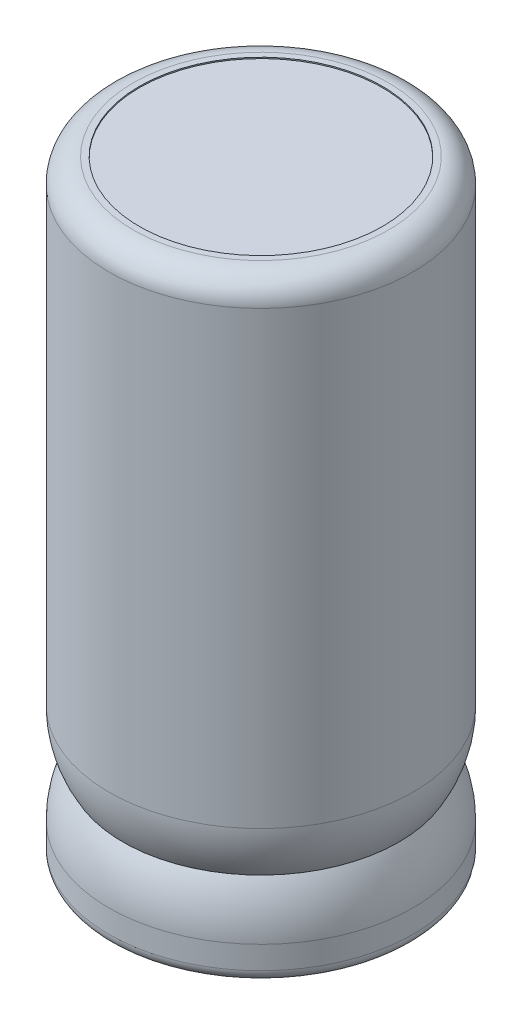
SolidWorks part; units mm, degrees
ref_plane "Front Plane" through (0, 0, 0) normal (0, 0, 1) x (1, 0, 0)
ref_plane "Top Plane" through (0, 0, 0) normal (0, 1, 0) x (1, 0, 0)
ref_plane "Right Plane" through (0, 0, 0) normal (1, 0, 0) x (0, 0, -1)
sketch "Sketch1" plane through (0, 0, 0) normal (0, 0, 1) x (1, 0, 0)
  line L0 (-6.35, 50.2) -> (-6.35, 0) construction
  line L1 (-6.35, 0.1) -> (3.65, 0.1)
  line L2 (3.65, 50.2) -> (4.15, 50.2)
  line L3 (3.65, 0.1) -> (3.65, 0)
  line L4 (3.65, 0) -> (5.15, 0)
  line L5 (6.15, 48.2) -> (6.15, 11.13)
  line L6 (6.15, 2.88) -> (6.15, 1)
  line L7 (-6.35, 50.1) -> (-6.35, 0.1)
  line L8 (-6.35, 50.1) -> (3.65, 50.1)
  line L9 (3.65, 50.1) -> (3.65, 50.2)
  arc A0 (4.15, 50.2) -> (6.15, 48.2) centre (4.15, 48.2) cw
  arc A3 (5.15, 0) -> (6.15, 1) centre (5.15, 1) ccw
  arc A4 (6.15, 2.88) -> (5.0045, 7.005) centre (-1.85, 2.88) ccw
  arc A5 (5.0045, 7.005) -> (6.15, 11.13) centre (-1.85, 11.13) ccw
  point P9 (6.15, 50.2)
  point P18 (6.15, 0)
  dimension "D4" = 2
  dimension "D5" = 8.25
  dimension "D7" = 8
  dimension "D1" = 1
  dimension "D2" = 12.5
  dimension "D3" = 50.2
  dimension "D6" = 1.88
  dimension "D8" = 10
  dimension "D9" = 0.1
  dimension "D10" = 6.15
  dimension "D11" = 10
  dimension "D12" = 0.1
revolve "Base-Revolve" add sketch "Sketch1" angle 360 about L0
sketch "Sketch2" plane through (0, 0.1, 0) normal (0, -1, 0) x (1, 0, 0)
  line L0 (0, 0) -> (-18.087, 0) construction
  circle A0 centre (0, 0) radius 0.5
  circle A1 centre (-12.7, 0) radius 0.5
  circle A2 centre (-6.35, 0) radius 10 construction
  circle A3 centre (-6.35, 0) radius 6.35 construction
  point P6 (-6.35, 0)
  dimension "D1" = 1
extrude "Boss-Extrude1" add sketch "Sketch2" along normal blind 3.5
ref_plane "Board Plane" through (0, -0.3, 0) normal (0, 1, 0) x (-1, 0, 0)
sketch "Component_Outline" plane through (0, -0.3, 0) normal (0, 1, 0) x (-1, 0, 0)
  circle A0 centre (6.35, 0) radius 12.5
  circle A1 centre (6.35, 0) radius 12.5 construction
  point P4 (0, 0)
